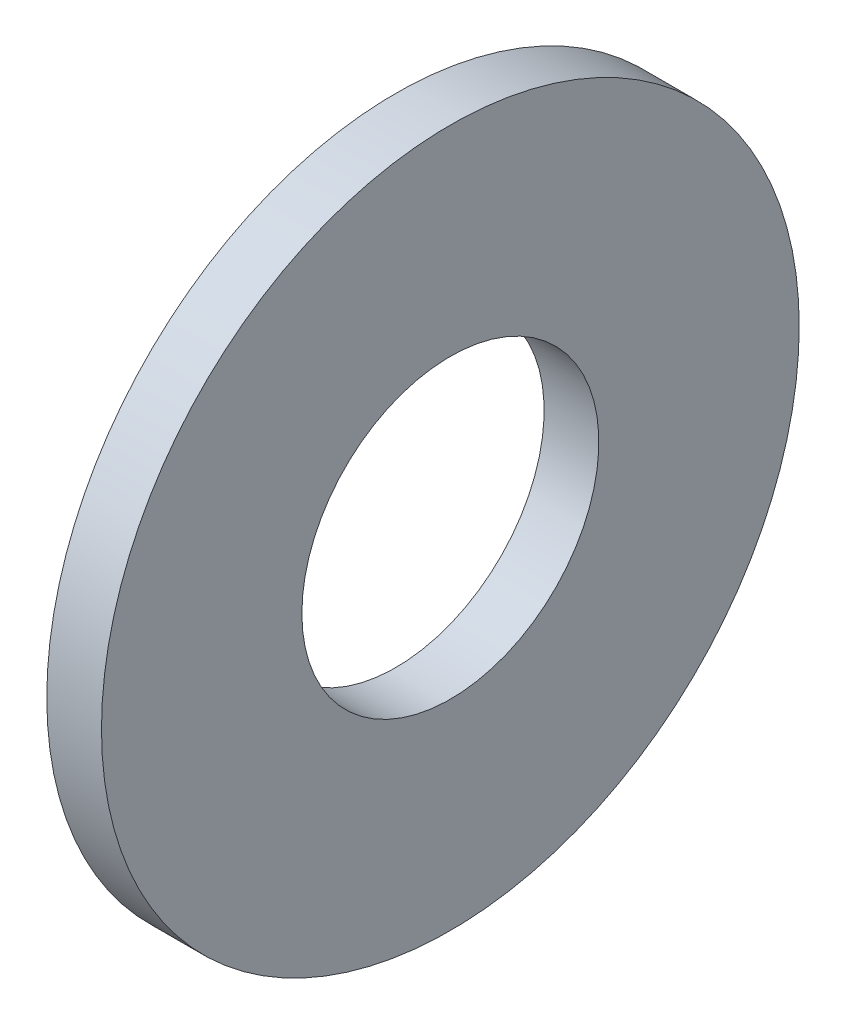
SolidWorks part; units mm, degrees
ref_plane "Plane1" through (0, 0, 0) normal (0, 0, 1) x (1, 0, 0)
ref_plane "Plane2" through (0, 0, 0) normal (0, 1, 0) x (1, 0, 0)
ref_plane "Plane3" through (0, 0, 0) normal (1, 0, 0) x (0, 0, -1)
sketch "Sketch1" plane through (0, 0, 0) normal (0, 0, 1) x (1, 0, 0)
  line L0 (-34.925, 0) -> (9.525, 0) construction
  line L1 (0, 3.3782) -> (0, 7.9375)
  line L2 (0, 7.9375) -> (-1.2446, 7.9375)
  line L3 (-1.2446, 7.9375) -> (-1.2446, 3.3782)
  line L4 (-1.2446, 3.3782) -> (0, 3.3782)
  dimension "Thickness" = 1.2446
  dimension "Inside_dia" = 6.7564
  dimension "Outside_dia" = 15.875
revolve "Base-Revolve" add sketch "Sketch1" angle 360 about L0
